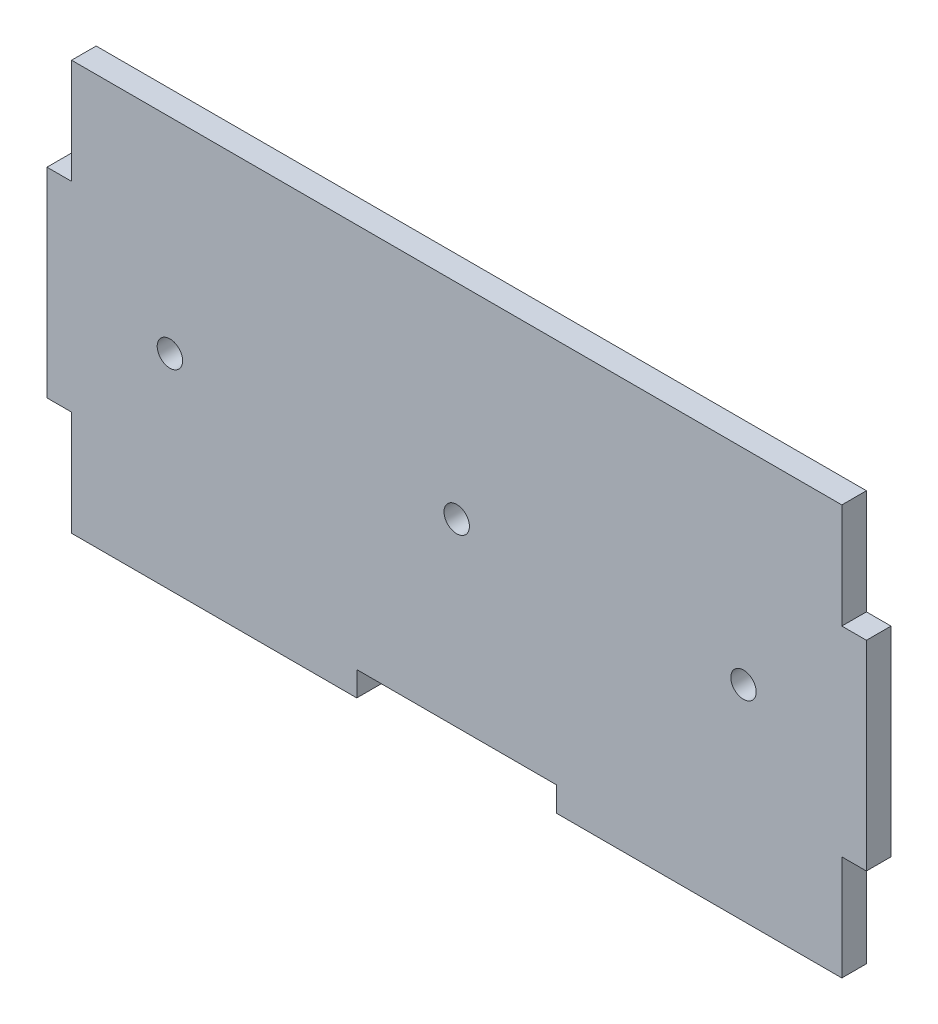
SolidWorks part; units mm, degrees
ref_plane "Alzado" through (0, 0, 0) normal (0, 0, 1) x (1, 0, 0)
ref_plane "Planta" through (0, 0, 0) normal (0, 1, 0) x (1, 0, 0)
ref_plane "Vista lateral" through (0, 0, 0) normal (1, 0, 0) x (0, 0, -1)
sketch "Model" plane through (0, 0, 0) normal (0, 0, 1) x (1, 0, 0)
  line L0 (186, 103) -> (186, 90.195)
  line L1 (186, 90.195) -> (183, 90.195)
  line L2 (183, 90.195) -> (183, 65.805)
  line L3 (183, 65.805) -> (186, 65.805)
  line L4 (186, 65.805) -> (186, 53)
  line L5 (186, 53) -> (220.805, 53)
  line L6 (220.805, 53) -> (220.805, 56)
  line L7 (220.805, 56) -> (245.195, 56)
  line L8 (245.195, 56) -> (245.195, 53)
  line L9 (245.195, 53) -> (269.585, 53)
  line L10 (269.585, 53) -> (280, 53)
  line L11 (280, 53) -> (280, 65.805)
  line L12 (280, 65.805) -> (283, 65.805)
  line L13 (283, 65.805) -> (283, 90.195)
  line L14 (283, 90.195) -> (280, 90.195)
  line L15 (280, 90.195) -> (280, 103)
  line L16 (280, 103) -> (186, 103)
extrude "Saliente-Extruir1" add sketch "Model" along normal blind 3
sketch "Croquis1" plane through (0, 0, 3) normal (0, 0, 1) x (1, 0, 0)
  line L0 (233, 56) -> (233, 103) construction
  line L1 (220.805, 56) -> (245.195, 56) construction
  line L2 (280, 103) -> (186, 103) construction
  line L3 (183, 78) -> (283, 78) construction
  line L4 (183, 90.195) -> (183, 65.805) construction
  line L5 (283, 65.805) -> (283, 90.195) construction
  circle A0 centre (233, 78) radius 1.55
  circle A1 centre (198, 78) radius 1.55
  circle A2 centre (268, 78) radius 1.55
  dimension "D1" = 3.1
  dimension "D2" = 3.1
  dimension "D3" = 3.1
  dimension "D4" = 35
  dimension "D5" = 35
extrude "Cortar-Extruir1" cut sketch "Croquis1" against normal blind 10
sketch "Croquis2" plane through (0, 0, 3) normal (0, 0, 1) x (1, 0, 0)
  line L0 (196.45, 78) -> (198, 78) construction
  line L1 (198, 78) -> (198, 76.45) construction
  line L2 (233, 76.45) -> (233, 78) construction
  line L3 (233, 78) -> (231.45, 78) construction
  line L4 (266.45, 78) -> (268, 78) construction
  line L5 (268, 78) -> (268, 76.45) construction
  circle A0 centre (198, 78) radius 1.55 construction
  circle A1 centre (233, 78) radius 1.55 construction
  circle A2 centre (268, 78) radius 1.55 construction
